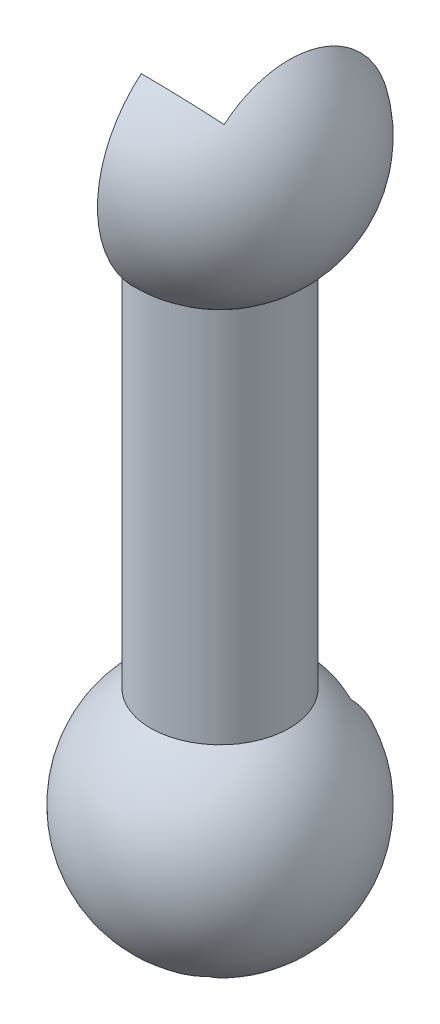
SolidWorks part; units mm, degrees
ref_plane "前视基准面" through (0, 0, 0) normal (0, 0, 1) x (1, 0, 0)
ref_plane "上视基准面" through (0, 0, 0) normal (0, 1, 0) x (1, 0, 0)
ref_plane "右视基准面" through (0, 0, 0) normal (1, 0, 0) x (0, 0, -1)
sketch "草图7" plane through (0, 0, 0) normal (0, 1, 0) x (1, 0, 0)
  line L14 (7.0315, 8.4457) -> (18.3717, 19.7859)
  line L38 (8.4457, 7.0315) -> (19.7859, 18.3717)
  line L57 (7.0315, -8.4457) -> (18.3717, -19.7859)
  line L58 (8.4457, -7.0315) -> (19.7859, -18.3717)
  line L61 (-8.4457, -7.0315) -> (-19.7859, -18.3717)
  line L62 (-7.0315, -8.4457) -> (-18.3717, -19.7859)
  line L65 (-8.4457, 7.0315) -> (-19.7859, 18.3717)
  line L66 (-7.0315, 8.4457) -> (-18.3717, 19.7859)
  line L68 (5, 5) -> (-5, -5) construction
  line L69 (-5, 5) -> (5, -5) construction
  line L70 (-5, 5) -> (5, 5) construction
  line L71 (1.127, 4) -> (-1.127, 4)
  line L73 (1.127, 6) -> (-1.127, 6)
  line L75 (1.127, 4) -> (-1.127, 6) construction
  line L76 (1.127, 6) -> (-1.127, 4) construction
  line L78 (4, -1.127) -> (4, 1.127)
  line L80 (6, -1.127) -> (6, 1.127)
  line L82 (-1.127, -4) -> (1.127, -4)
  line L84 (-1.127, -6) -> (1.127, -6)
  line L86 (-4, 1.127) -> (-4, -1.127)
  line L88 (-6, 1.127) -> (-6, -1.127)
  circle A1 centre (5, 5) radius 2
  circle A6 centre (0, 0) radius 30
  arc A7 (-19.7859, 18.3717) -> (-19.7859, -18.3717) centre (0, 0) ccw
  arc A8 (18.3717, 19.7859) -> (-18.3717, 19.7859) centre (0, 0) ccw
  arc A9 (19.7859, -18.3717) -> (19.7859, 18.3717) centre (0, 0) ccw
  circle A10 centre (5, -5) radius 2
  circle A11 centre (-5, -5) radius 2
  circle A12 centre (-5, 5) radius 2
  arc A13 (7.0315, 8.4457) -> (1.127, 6) centre (5, 5) ccw
  arc A14 (8.4457, -7.0315) -> (6, -1.127) centre (5, -5) ccw
  arc A15 (-7.0315, -8.4457) -> (-1.127, -6) centre (-5, -5) ccw
  arc A16 (-8.4457, 7.0315) -> (-6, 1.127) centre (-5, 5) ccw
  arc A17 (-18.3717, -19.7859) -> (18.3717, -19.7859) centre (0, 0) ccw
  arc A18 (-4, 1.127) -> (-1.127, 4) centre (-5, 5) ccw
  arc A19 (-6, -1.127) -> (-8.4457, -7.0315) centre (-5, -5) ccw
  arc A20 (4, -1.127) -> (1.127, -4) centre (5, -5) ccw
  arc A21 (6, 1.127) -> (8.4457, 7.0315) centre (5, 5) ccw
  arc A22 (-1.127, 6) -> (-7.0315, 8.4457) centre (-5, 5) ccw
  arc A23 (1.127, 4) -> (4, 1.127) centre (5, 5) ccw
  arc A24 (-1.127, -4) -> (-4, -1.127) centre (-5, -5) ccw
  arc A25 (1.127, -6) -> (7.0315, -8.4457) centre (5, -5) ccw
  point P0 (0, 0)
  point P2 (0, 5)
  point P21 (0, 0)
  point P22 (0, 0)
  point P34 (0, 0)
  point P47 (0, 0)
  point P60 (0, 0)
  dimension "D3" = 4
  dimension "D6" = 2
  dimension "D2" = 60
  dimension "D7" = 54
  dimension "D14" = 8
  dimension "D5" = 2
  dimension "D8" = 2
  dimension "D9" = 2
  dimension "D10" = 2
  dimension "D11" = 10
  dimension "D12" = 5
  dimension "D13" = 5
  dimension "D15" = 4
  dimension "D16" = 4
  dimension "D4" = 4
extrude "凸台-拉伸1" add sketch "草图7" along normal blind 178.35
sketch "草图8" plane through (0, 0, 0) normal (1, 0, 0) x (0, 0, -1)
  line L0 (30, 0) -> (30, 178.35) construction
  line L4 (0, 263.35) -> (0, 260.35)
  line L7 (0, 210.35) -> (0, 182.6378) construction
  line L8 (30, 170.35) -> (30, 166.6579)
  line L10 (30, 178.35) -> (-30, 178.35) construction
  line L11 (-23.7985, 210.35) -> (25.5416, 210.35) construction
  arc A4 (30, 166.6579) -> (0, 263.35) centre (0, 210.35) ccw
  arc A5 (30, 170.35) -> (0, 260.35) centre (0, 210.35) ccw
  dimension "D1" = 53
  dimension "D2" = 30
  dimension "D3" = 3
  dimension "D4" = 32
revolve "旋转1" add sketch "草图8" angle 180 about L7
sketch "草图12" plane through (0, 0, 0) normal (0, 0, 1) x (1, 0, 0)
  line L0 (-30.1315, 210.35) -> (27.988, 210.35)
  line L1 (18.3717, 178.35) -> (-18.3717, 178.35) construction
  dimension "D1" = 32
ref_plane "基准面2" through (0, 210.35, 0) normal (0, 1, 0) x (1, 0, 0)
sketch "草图13" plane through (0, 210.35, 0) normal (0, 1, 0) x (1, 0, 0)
  line L0 (-30.1315, 0) -> (27.988, 0) construction
  line L1 (29.9283, 32) -> (-32.0717, 32)
  line L2 (29.9283, 32) -> (29.9283, 95.4289)
  line L3 (29.9283, 95.4289) -> (-32.0717, 95.4289)
  line L4 (-32.0717, 32) -> (-32.0717, 95.4289)
  line L5 (-1.0717, 0) -> (-1.0717, 15.2558) construction
  dimension "D1" = 32
  dimension "D2" = 62
revolve "旋转2" add sketch "草图13" angle 130 about L0
combine bodies "组合1" operation type subtract main body 135 bodies to subtract 137
sketch "草图17" plane through (0, 0, 0) normal (1, 0, 0) x (0, 0, -1)
  line L0 (0, 0) -> (0, -56.1865) construction
  line L1 (-39.9777, -40) -> (39.9777, -40) construction
  line L2 (-30, 0) -> (30, 0) construction
  line L3 (0, -90) -> (0, -93)
  line L4 (30, 0) -> (30, 3.6921)
  arc A0 (0, -93) -> (30, 3.6921) centre (0, -40) ccw
  arc A1 (0, -90) -> (30, 0) centre (0, -40) ccw
  point P7 (0, -40)
  dimension "D2" = 106
  dimension "D1" = 40
revolve "旋转3" add sketch "草图17" angle 360 about L0
sketch "草图18" plane through (0, 0, 0) normal (0, 0, 1) x (1, 0, 0)
  line L0 (-67.879, -40) -> (78.6225, -40)
  line L1 (-30, 0) -> (30, 0) construction
  dimension "D1" = 40
ref_plane "基准面3" through (0, -40, 0) normal (0, 1, 0) x (1, 0, 0)
sketch "草图19" plane through (0, -40, 0) normal (0, 1, 0) x (1, 0, 0)
  line L1 (-22.5, 0) -> (22.5, 0)
  line L2 (-22.5, 0) -> (-22.5, 76.5374)
  line L3 (-22.5, 76.5374) -> (22.5, 76.5374)
  line L4 (22.5, 0) -> (22.5, 76.5374)
  line L5 (0, 0) -> (0, 79.9293) construction
  dimension "D1" = 45
revolve "旋转4" add sketch "草图19" angle 45 about L0
combine bodies "组合2" operation type subtract main body 139 bodies to subtract 140
sketch "折弯-线1" plane through (0, 0, 0) normal (0, 1, 0) x (1, 0, 0)
sketch "边界框1" plane through (0, 0, 0) normal (0, 1, 0) x (1, 0, 0)
